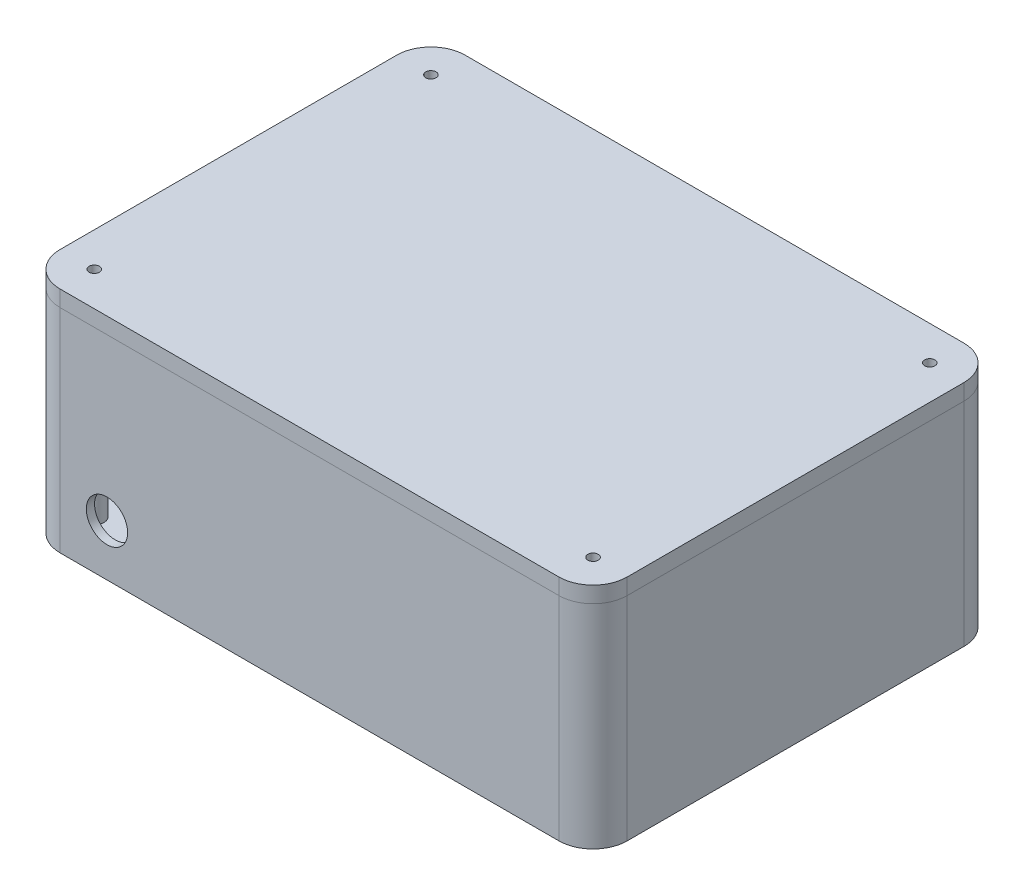
SolidWorks part; units mm, degrees
material "ABS"
ref_plane "Front Plane" through (0, 0, 0) normal (0, 0, 1) x (1, 0, 0)
ref_plane "Top Plane" through (0, 0, 0) normal (0, 1, 0) x (1, 0, 0)
ref_plane "Right Plane" through (0, 0, 0) normal (1, 0, 0) x (0, 0, -1)
sketch "Sketch1" plane through (0, 0, 0) normal (0, 1, 0) x (1, 0, 0)
  line L0 (-76.6347, 59.69) -> (76.6347, 59.69)
  line L1 (-76.6347, 62.23) -> (76.6347, 62.23)
  line L2 (-87.1347, 51.73) -> (-87.1347, -51.73)
  line L3 (-76.6347, -62.23) -> (76.6347, -62.23)
  line L4 (87.1347, 51.73) -> (87.1347, -51.73)
  line L5 (-87.1347, 62.23) -> (87.1347, -62.23) construction
  line L6 (-87.1347, -62.23) -> (87.1347, 62.23) construction
  line L7 (84.5947, 51.73) -> (84.5947, -51.73)
  line L8 (-76.6347, -59.69) -> (76.6347, -59.69)
  line L9 (-84.5947, 51.73) -> (-84.5947, -51.73)
  arc A0 (-87.1347, -51.73) -> (-76.6347, -62.23) centre (-76.6347, -51.73) ccw
  arc A1 (76.6347, -62.23) -> (87.1347, -51.73) centre (76.6347, -51.73) ccw
  arc A2 (76.6347, 62.23) -> (87.1347, 51.73) centre (76.6347, 51.73) cw
  arc A3 (-76.6347, 62.23) -> (-87.1347, 51.73) centre (-76.6347, 51.73) ccw
  arc A4 (76.6347, 59.69) -> (84.5947, 51.73) centre (76.6347, 51.73) cw
  arc A5 (76.6347, -59.69) -> (84.5947, -51.73) centre (76.6347, -51.73) ccw
  arc A6 (-84.5947, -51.73) -> (-76.6347, -59.69) centre (-76.6347, -51.73) ccw
  arc A7 (-76.6347, 59.69) -> (-84.5947, 51.73) centre (-76.6347, 51.73) ccw
  circle A8 centre (-76.6347, 51.73) radius 1.5875
  circle A9 centre (-76.6347, 51.73) radius 2.9845
  circle A10 centre (76.6347, 51.73) radius 1.5875
  circle A11 centre (76.6347, 51.73) radius 2.9845
  circle A12 centre (76.6347, -51.73) radius 1.5875
  circle A13 centre (76.6347, -51.73) radius 2.9845
  circle A14 centre (-76.6347, -51.73) radius 1.5875
  circle A15 centre (-76.6347, -51.73) radius 2.9845
  point P0 (0, 0)
  dimension "D3" = 10.5
  dimension "D5" = 5.969
  dimension "D6" = 3.175
  dimension "D1" = 124.46
  dimension "D2" = 174.2694
  dimension "D4" = 2.54
extrude "Sides" add sketch "Sketch1" along normal blind 60.96 contours L1 A3 L2 A0 L3 A1 L4 A2 A7 L0 A4 L7 A5 L8 A6 L9 | A9 A8 | A11 A10 | A13 A12 | A15 A14
sketch "Sketch2" plane through (0, 0, 0) normal (0, 1, 0) x (1, 0, 0)
  line L4 (-76.6347, -62.23) -> (76.6347, -62.23) construction
  line L5 (87.1347, 51.73) -> (87.1347, -51.73) construction
  line L6 (-76.6347, 62.23) -> (76.6347, 62.23) construction
  line L7 (-87.1347, 51.73) -> (-87.1347, -51.73) construction
  line L8 (-76.6347, -62.23) -> (76.6347, -62.23)
  line L9 (87.1347, 51.73) -> (87.1347, -51.73)
  line L10 (-76.6347, 62.23) -> (76.6347, 62.23)
  line L11 (-87.1347, 51.73) -> (-87.1347, -51.73)
  arc A4 (-87.1347, -51.73) -> (-76.6347, -62.23) centre (-76.6347, -51.73) ccw construction
  arc A5 (76.6347, -62.23) -> (87.1347, -51.73) centre (76.6347, -51.73) ccw construction
  arc A6 (87.1347, 51.73) -> (76.6347, 62.23) centre (76.6347, 51.73) ccw construction
  arc A7 (-76.6347, 62.23) -> (-87.1347, 51.73) centre (-76.6347, 51.73) ccw construction
  arc A8 (-87.1347, -51.73) -> (-76.6347, -62.23) centre (-76.6347, -51.73) ccw
  arc A9 (76.6347, -62.23) -> (87.1347, -51.73) centre (76.6347, -51.73) ccw
  arc A10 (87.1347, 51.73) -> (76.6347, 62.23) centre (76.6347, 51.73) ccw
  arc A11 (-76.6347, 62.23) -> (-87.1347, 51.73) centre (-76.6347, 51.73) ccw
extrude "Bottom" add sketch "Sketch2" against normal blind 4.318
sketch "Sketch3" plane through (0, 60.96, 0) normal (0, 1, 0) x (1, 0, 0)
  line L0 (-87.1347, 51.73) -> (-87.1347, -51.73) construction
  line L1 (-76.6347, 62.23) -> (76.6347, 62.23) construction
  line L2 (87.1347, 51.73) -> (87.1347, -51.73) construction
  line L3 (-76.6347, -62.23) -> (76.6347, -62.23) construction
  line L4 (-87.1347, 51.73) -> (-87.1347, -51.73)
  line L5 (-76.6347, 62.23) -> (76.6347, 62.23)
  line L6 (87.1347, 51.73) -> (87.1347, -51.73)
  line L7 (-76.6347, -62.23) -> (76.6347, -62.23)
  arc A0 (-76.6347, 62.23) -> (-87.1347, 51.73) centre (-76.6347, 51.73) ccw construction
  arc A1 (87.1347, 51.73) -> (76.6347, 62.23) centre (76.6347, 51.73) ccw construction
  arc A2 (76.6347, -62.23) -> (87.1347, -51.73) centre (76.6347, -51.73) ccw construction
  arc A3 (-87.1347, -51.73) -> (-76.6347, -62.23) centre (-76.6347, -51.73) ccw construction
  arc A4 (-76.6347, 62.23) -> (-87.1347, 51.73) centre (-76.6347, 51.73) ccw
  arc A5 (87.1347, 51.73) -> (76.6347, 62.23) centre (76.6347, 51.73) ccw
  arc A6 (76.6347, -62.23) -> (87.1347, -51.73) centre (76.6347, -51.73) ccw
  arc A7 (-87.1347, -51.73) -> (-76.6347, -62.23) centre (-76.6347, -51.73) ccw
  circle A8 centre (76.6347, 51.73) radius 1.5875 construction
  circle A9 centre (76.6347, -51.73) radius 1.5875 construction
  circle A10 centre (-76.6347, -51.73) radius 1.5875 construction
  circle A11 centre (-76.6347, 51.73) radius 1.5875 construction
  circle A12 centre (76.6347, 51.73) radius 1.5875
  circle A13 centre (76.6347, -51.73) radius 1.5875
  circle A14 centre (-76.6347, -51.73) radius 1.5875
  circle A15 centre (-76.6347, 51.73) radius 1.5875
extrude "Lid" add sketch "Sketch3" along normal blind 4.953 separate body
sketch "Sketch6" plane through (-87.1347, 0, 0) normal (-1, 0, 0) x (0, 0, 1)
  line L4 (51.73, 60.96) -> (51.73, -4.318) construction
  line L5 (-51.73, 60.96) -> (51.73, 60.96) construction
  line L6 (-51.73, 60.96) -> (-51.73, -4.318) construction
  line B0 (4.74, 41.91) -> (44.11, 41.91) construction
  line B1 (15.408, 50.927) -> (33.442, 50.927) construction
  line B2 (9.693, 45.212) -> (9.693, 38.608)
  line B3 (15.408, 32.893) -> (33.442, 32.893)
  line B4 (39.157, 45.212) -> (39.157, 38.608)
  circle B5 centre (4.74, 41.91) radius 1.778
  circle B6 centre (44.11, 41.91) radius 1.778
  arc B7 (33.442, 32.893) -> (39.157, 38.608) centre (33.442, 38.608) ccw
  arc B8 (9.693, 38.608) -> (15.408, 32.893) centre (15.408, 38.608) ccw
  line B9 (22.8375, 52.832) -> (26.0125, 52.832)
  arc B10 (22.8375, 52.832) -> (20.9325, 50.927) centre (22.8375, 50.927) ccw
  arc B11 (26.0125, 52.832) -> (27.9175, 50.927) centre (26.0125, 50.927) cw
  line B12 (40.2345, 47.6135) -> (38.8302, 47.117)
  arc B13 (39.1338, 50.7267) -> (40.2345, 47.6135) centre (39.6842, 49.1701) cw
  line B14 (36.7391, 49.88) -> (39.1338, 50.7267)
  line B15 (9.7162, 50.7267) -> (12.1109, 49.88)
  arc B16 (8.6155, 47.6135) -> (9.7162, 50.7267) centre (9.1658, 49.1701) cw
  line B17 (10.0198, 47.117) -> (8.6155, 47.6135)
  line B18 (15.408, 50.927) -> (20.9325, 50.927)
  line B19 (27.9175, 50.927) -> (33.442, 50.927)
  arc B20 (15.408, 50.927) -> (12.1109, 49.88) centre (15.408, 45.212) ccw
  arc B21 (10.0198, 47.117) -> (9.693, 45.212) centre (15.408, 45.212) ccw
  arc B22 (33.442, 50.927) -> (36.7391, 49.88) centre (33.442, 45.212) cw
  arc B23 (38.8302, 47.117) -> (39.157, 45.212) centre (33.442, 45.212) cw
  line B24 (-44.11, 41.91) -> (-4.74, 41.91) construction
  line B25 (-39.157, 45.212) -> (-39.157, 38.608)
  line B26 (-33.442, 32.893) -> (-15.408, 32.893)
  line B27 (-9.693, 45.212) -> (-9.693, 38.608)
  circle B28 centre (-44.11, 41.91) radius 1.778
  circle B29 centre (-4.74, 41.91) radius 1.778
  arc B30 (-15.408, 32.893) -> (-9.693, 38.608) centre (-15.408, 38.608) ccw
  arc B31 (-39.157, 38.608) -> (-33.442, 32.893) centre (-33.442, 38.608) ccw
  line B32 (-26.0125, 52.832) -> (-22.8375, 52.832)
  arc B33 (-26.0125, 52.832) -> (-27.9175, 50.927) centre (-26.0125, 50.927) ccw
  arc B34 (-22.8375, 52.832) -> (-20.9325, 50.927) centre (-22.8375, 50.927) cw
  line B35 (-8.6155, 47.6135) -> (-10.0198, 47.117)
  arc B36 (-9.7162, 50.7267) -> (-8.6155, 47.6135) centre (-9.1658, 49.1701) cw
  line B37 (-12.1109, 49.88) -> (-9.7162, 50.7267)
  line B38 (-39.1338, 50.7267) -> (-36.7391, 49.88)
  arc B39 (-40.2345, 47.6135) -> (-39.1338, 50.7267) centre (-39.6842, 49.1701) cw
  line B40 (-38.8302, 47.117) -> (-40.2345, 47.6135)
  line B41 (-33.442, 50.927) -> (-27.9175, 50.927)
  line B42 (-20.9325, 50.927) -> (-15.408, 50.927)
  arc B43 (-33.442, 50.927) -> (-36.7391, 49.88) centre (-33.442, 45.212) ccw
  arc B44 (-38.8302, 47.117) -> (-39.157, 45.212) centre (-33.442, 45.212) ccw
  arc B45 (-15.408, 50.927) -> (-12.1109, 49.88) centre (-15.408, 45.212) cw
  arc B46 (-10.0198, 47.117) -> (-9.693, 45.212) centre (-15.408, 45.212) cw
  line B47 (-44.11, 13.97) -> (-4.74, 13.97) construction
  line B48 (-39.157, 17.272) -> (-39.157, 10.668)
  line B49 (-33.442, 4.953) -> (-15.408, 4.953)
  line B50 (-9.693, 17.272) -> (-9.693, 10.668)
  circle B51 centre (-44.11, 13.97) radius 1.778
  circle B52 centre (-4.74, 13.97) radius 1.778
  arc B53 (-15.408, 4.953) -> (-9.693, 10.668) centre (-15.408, 10.668) ccw
  arc B54 (-39.157, 10.668) -> (-33.442, 4.953) centre (-33.442, 10.668) ccw
  line B55 (-26.0125, 24.892) -> (-22.8375, 24.892)
  arc B56 (-26.0125, 24.892) -> (-27.9175, 22.987) centre (-26.0125, 22.987) ccw
  arc B57 (-22.8375, 24.892) -> (-20.9325, 22.987) centre (-22.8375, 22.987) cw
  line B58 (-8.6155, 19.6735) -> (-10.0198, 19.177)
  arc B59 (-9.7162, 22.7867) -> (-8.6155, 19.6735) centre (-9.1658, 21.2301) cw
  line B60 (-12.1109, 21.94) -> (-9.7162, 22.7867)
  line B61 (-39.1338, 22.7867) -> (-36.7391, 21.94)
  arc B62 (-40.2345, 19.6735) -> (-39.1338, 22.7867) centre (-39.6842, 21.2301) cw
  line B63 (-38.8302, 19.177) -> (-40.2345, 19.6735)
  line B64 (-33.442, 22.987) -> (-27.9175, 22.987)
  line B65 (-20.9325, 22.987) -> (-15.408, 22.987)
  arc B66 (-33.442, 22.987) -> (-36.7391, 21.94) centre (-33.442, 17.272) ccw
  arc B67 (-38.8302, 19.177) -> (-39.157, 17.272) centre (-33.442, 17.272) ccw
  arc B68 (-15.408, 22.987) -> (-12.1109, 21.94) centre (-15.408, 17.272) cw
  arc B69 (-10.0198, 19.177) -> (-9.693, 17.272) centre (-15.408, 17.272) cw
  line B70 (4.74, 13.97) -> (44.11, 13.97) construction
  line B71 (9.693, 17.272) -> (9.693, 10.668)
  line B72 (15.408, 4.953) -> (33.442, 4.953)
  line B73 (39.157, 17.272) -> (39.157, 10.668)
  circle B74 centre (4.74, 13.97) radius 1.778
  circle B75 centre (44.11, 13.97) radius 1.778
  arc B76 (33.442, 4.953) -> (39.157, 10.668) centre (33.442, 10.668) ccw
  arc B77 (9.693, 10.668) -> (15.408, 4.953) centre (15.408, 10.668) ccw
  line B78 (22.8375, 24.892) -> (26.0125, 24.892)
  arc B79 (22.8375, 24.892) -> (20.9325, 22.987) centre (22.8375, 22.987) ccw
  arc B80 (26.0125, 24.892) -> (27.9175, 22.987) centre (26.0125, 22.987) cw
  line B81 (40.2345, 19.6735) -> (38.8302, 19.177)
  arc B82 (39.1338, 22.7867) -> (40.2345, 19.6735) centre (39.6842, 21.2301) cw
  line B83 (36.7391, 21.94) -> (39.1338, 22.7867)
  line B84 (9.7162, 22.7867) -> (12.1109, 21.94)
  arc B85 (8.6155, 19.6735) -> (9.7162, 22.7867) centre (9.1658, 21.2301) cw
  line B86 (10.0198, 19.177) -> (8.6155, 19.6735)
  line B87 (15.408, 22.987) -> (20.9325, 22.987)
  line B88 (27.9175, 22.987) -> (33.442, 22.987)
  arc B89 (15.408, 22.987) -> (12.1109, 21.94) centre (15.408, 17.272) ccw
  arc B90 (10.0198, 19.177) -> (9.693, 17.272) centre (15.408, 17.272) ccw
  arc B91 (33.442, 22.987) -> (36.7391, 21.94) centre (33.442, 17.272) cw
  arc B92 (38.8302, 19.177) -> (39.157, 17.272) centre (33.442, 17.272) cw
sketch_block_instance "Molex MX150 Panel Mount-8"
sketch_block "Molex MX150 Panel Mount" parameters "D1"=3.556, "D3"=5.715, "D12"=2.2522, "D2"=39.37, "D4"=17.78, "D5"=6.35, "D6"=3.8381, "D7"=3.8381, "D8"=2.0786, "D9"=3.5188, "D10"=3.6262, "D11"=0.691, "D13"=18.034
sketch_block_instance "Molex MX150 Panel Mount-10"
sketch_block_instance "Molex MX150 Panel Mount-11"
sketch_block_instance "Molex MX150 Panel Mount-12" parameters "D1"=52.6921, "D2"=47.625, "D3"=21.6382, "D4"=65.278
extrude "MX150 Cuts" cut sketch "Sketch6" against normal up to next (2.54 mm away)
sketch "Entry Holes" plane through (-87.1347, 0, 0) normal (-1, 0, 0) x (0, 0, 1)
  line L0 (-33.442, 32.893) -> (-15.408, 32.893) construction
  line L1 (-9.693, 38.608) -> (-9.693, 45.212) construction
  line L2 (-9.693, 10.668) -> (-9.693, 17.272) construction
  line L3 (26.0125, 52.832) -> (22.8375, 52.832) construction
  circle A0 centre (-24.425, 41.91) radius 1.5875
  circle A1 centre (24.425, 41.91) radius 1.5875
  circle A2 centre (24.425, 13.97) radius 1.5875
  circle A3 centre (-24.425, 13.97) radius 1.5875
  point P10 (-24.425, 32.893)
  point P13 (-9.693, 41.91)
  point P16 (-9.693, 13.97)
  point P19 (24.425, 52.832)
  dimension "D1" = 3.175
sketch "Sketch7" plane through (0, 0, 62.23) normal (0, 0, 1) x (1, 0, 0)
  line L0 (-76.6347, 0) -> (76.6347, 0) construction
  line L2 (-73.6502, 60.96) -> (-79.6192, 60.96) construction
  line L3 (-73.6502, 60.96) -> (-79.6192, 60.96)
  circle A0 centre (-62.2202, 11.43) radius 6.35
  dimension "D1" = 12.7
  dimension "D2" = 11.43
  dimension "D3" = 11.43
extrude "Cut-Extrude1" cut sketch "Sketch7" against normal up to next (2.54 mm away) contours A0
